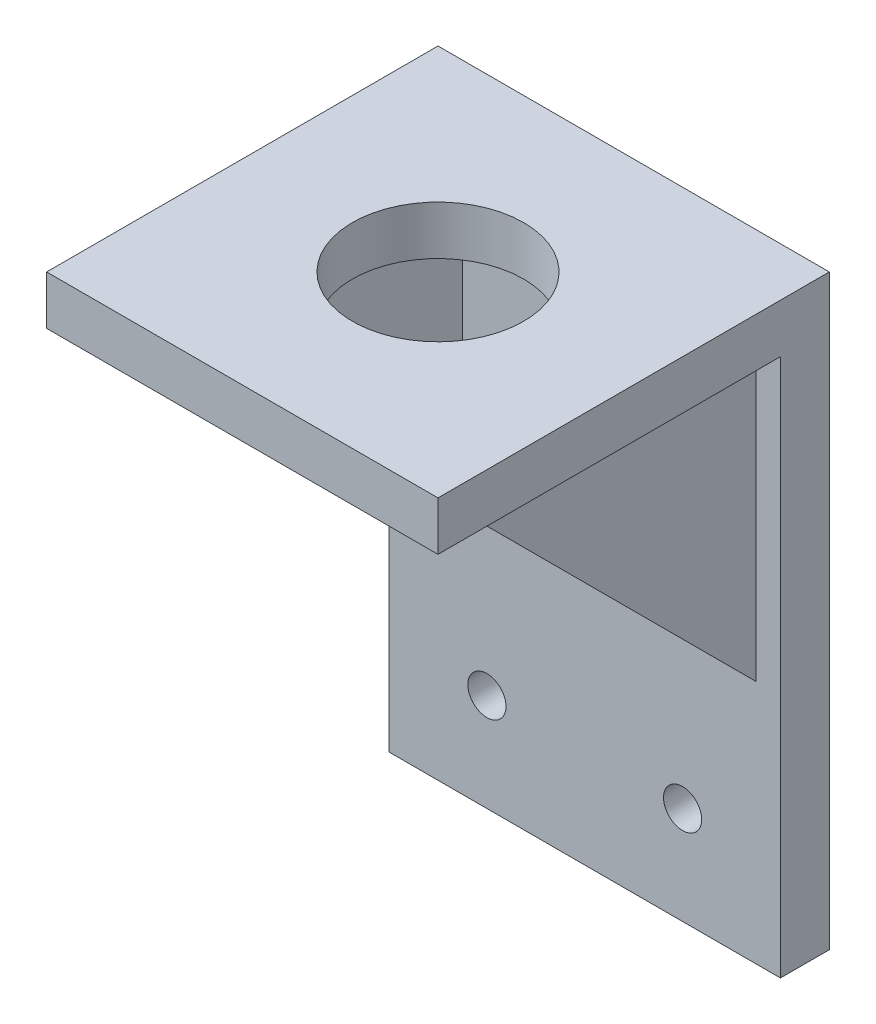
SolidWorks part; units mm, degrees
ref_plane "Front Plane" through (0, 0, 0) normal (0, 0, 1) x (1, 0, 0)
ref_plane "Top Plane" through (0, 0, 0) normal (0, 1, 0) x (1, 0, 0)
ref_plane "Right Plane" through (0, 0, 0) normal (1, 0, 0) x (0, 0, -1)
sketch "Sketch1" plane through (0, 0, 0) normal (0, 0, 1) x (1, 0, 0)
  line L1 (-25.4, -38.1) -> (25.4, -38.1)
  line L2 (-25.4, -38.1) -> (-25.4, 38.1)
  line L3 (-25.4, 38.1) -> (25.4, 38.1)
  line L4 (25.4, -38.1) -> (25.4, 38.1)
  line L5 (-25.4, -38.1) -> (25.4, 38.1) construction
  line L6 (-25.4, 38.1) -> (25.4, -38.1) construction
  circle A0 centre (-12.7, -25.4) radius 2.4765
  circle A1 centre (12.7, -25.4) radius 2.4765
  circle A2 centre (0, 25.4) radius 2.4765
  point P0 (0, 0)
  point P12 (0, 0)
  point P13 (0, 0)
  point P14 (0, 0)
  dimension "D3" = 4.953
  dimension "D1" = 50.8
  dimension "D2" = 76.2
  dimension "D4" = 12.7
  dimension "D5" = 12.7
  dimension "D6" = 12.7
  dimension "D7" = 12.7
extrude "Boss-Extrude1" add sketch "Sketch1" along normal blind 6.35
sketch "Sketch2" plane through (0, 0, 0) normal (0, 0, -1) x (-1, 0, 0)
  line L0 (-25.4, -38.1) -> (-25.4, 38.1) construction
  line L1 (25.4, 38.1) -> (25.4, -38.1) construction
  line L2 (-25.4, 38.1) -> (25.4, 38.1) construction
  arc A0 (-4.7625, 13.4704) -> (-9.2844, 10.8596) centre (0, 0) ccw
  arc A1 (-14.2576, 10.0826) -> (-15.8606, 7.3061) centre (0, 0) ccw
  arc A2 (4.7625, 13.4704) -> (3.3331, 15.4918) centre (5.4772, 15.4918) cw
  arc A3 (3.3331, 15.4918) -> (1.603, 17.3888) centre (1.4281, 15.4918) ccw
  arc A4 (-4.7625, 13.4704) -> (-3.3331, 15.4918) centre (-5.4772, 15.4918) ccw
  arc A5 (-1.603, 17.3888) -> (-3.3331, 15.4918) centre (-1.4281, 15.4918) ccw
  arc A6 (14.2576, 10.0826) -> (11.7497, 10.6325) centre (12.7022, 8.9827) ccw
  arc A7 (9.2844, 10.8596) -> (11.7497, 10.6325) centre (10.6777, 12.4893) ccw
  arc A8 (15.0829, 4.8593) -> (15.8606, 7.3061) centre (14.1304, 6.5091) ccw
  arc A9 (14.0469, 2.6107) -> (15.0829, 4.8593) centre (16.1549, 3.0025) cw
  arc A10 (15.8606, -7.3061) -> (15.0829, -4.8593) centre (14.1304, -6.5091) ccw
  arc A11 (14.0469, -2.6107) -> (15.0829, -4.8593) centre (16.1549, -3.0025) ccw
  arc A12 (11.7497, -10.6325) -> (14.2576, -10.0826) centre (12.7022, -8.9827) ccw
  arc A13 (9.2844, -10.8596) -> (11.7497, -10.6325) centre (10.6777, -12.4893) cw
  arc A14 (1.603, -17.3888) -> (3.3331, -15.4918) centre (1.4281, -15.4918) ccw
  arc A15 (4.7625, -13.4704) -> (3.3331, -15.4918) centre (5.4772, -15.4918) ccw
  arc A16 (-3.3331, -15.4918) -> (-1.603, -17.3888) centre (-1.4281, -15.4918) ccw
  arc A17 (-4.7625, -13.4704) -> (-3.3331, -15.4918) centre (-5.4772, -15.4918) cw
  arc A18 (-14.2576, -10.0826) -> (-11.7497, -10.6325) centre (-12.7022, -8.9827) ccw
  arc A19 (-9.2844, -10.8596) -> (-11.7497, -10.6325) centre (-10.6777, -12.4893) ccw
  arc A20 (-15.0829, -4.8593) -> (-15.8606, -7.3061) centre (-14.1304, -6.5091) ccw
  arc A21 (-14.0469, -2.6107) -> (-15.0829, -4.8593) centre (-16.1549, -3.0025) cw
  arc A22 (-15.8606, 7.3061) -> (-15.0829, 4.8593) centre (-14.1304, 6.5091) ccw
  arc A23 (-14.0469, 2.6107) -> (-15.0829, 4.8593) centre (-16.1549, 3.0025) ccw
  arc A24 (-11.7497, 10.6325) -> (-14.2576, 10.0826) centre (-12.7022, 8.9827) ccw
  arc A25 (-9.2844, 10.8596) -> (-11.7497, 10.6325) centre (-10.6777, 12.4893) cw
  arc A26 (1.603, 17.3888) -> (-1.603, 17.3888) centre (0, 0) ccw
  arc A27 (15.8606, 7.3061) -> (14.2576, 10.0826) centre (0, 0) ccw
  arc A28 (14.2576, -10.0826) -> (15.8606, -7.3061) centre (0, 0) ccw
  arc A29 (-1.603, -17.3888) -> (1.603, -17.3888) centre (0, 0) ccw
  arc A30 (-15.8606, -7.3061) -> (-14.2576, -10.0826) centre (0, 0) ccw
  arc A31 (-14.0469, 2.6107) -> (-14.0469, -2.6107) centre (0, 0) ccw
  arc A32 (-9.2844, -10.8596) -> (-4.7625, -13.4704) centre (0, 0) ccw
  arc A33 (4.7625, -13.4704) -> (9.2844, -10.8596) centre (0, 0) ccw
  arc A34 (14.0469, -2.6107) -> (14.0469, 2.6107) centre (0, 0) ccw
  arc A35 (9.2844, 10.8596) -> (4.7625, 13.4704) centre (0, 0) ccw
  circle A36 centre (-12.7, 25.4) radius 2.2225
  circle A37 centre (12.7, 25.4) radius 2.2225
  point P67 (0, 0)
  point P73 (0, 0)
  dimension "D1" = 28.575
  dimension "D2" = 34.925
  dimension "D4" = 1.905
  dimension "D9" = 4.445
  dimension "D3" = 9.525
  dimension "D6" = 12.7
  dimension "D7" = 12.7
  dimension "D8" = 12.7
  dimension "D5" = 6
extrude "Boss-Extrude2" add sketch "Sketch2" along normal blind 3.175
sketch "Sketch3" plane through (0, 0, -3.175) normal (0, 0, -1) x (-1, 0, 0)
  line L1 (-3.175, -1.5875) -> (3.175, -1.5875)
  line L2 (-3.175, -1.5875) -> (-3.175, 1.5875)
  line L3 (-3.175, 1.5875) -> (3.175, 1.5875)
  line L4 (3.175, -1.5875) -> (3.175, 1.5875)
  line L5 (-3.175, -1.5875) -> (3.175, 1.5875) construction
  line L6 (-3.175, 1.5875) -> (3.175, -1.5875) construction
  point P0 (0, 0)
  dimension "D1" = 6.35
  dimension "D2" = 3.175
extrude "Cut-Extrude1" cut sketch "Sketch3" against normal through all
sketch "Sketch4" plane through (0, 38.1, 0) normal (0, 1, 0) x (1, 0, 0)
  line L0 (25.4, 0) -> (-25.4, 0) construction
  line L1 (-25.4, -6.35) -> (25.4, -6.35)
  line L2 (-25.4, -6.35) -> (-25.4, -50.8)
  line L3 (-25.4, -50.8) -> (25.4, -50.8)
  line L4 (25.4, -6.35) -> (25.4, -50.8)
  dimension "D1" = 50.8
extrude "Boss-Extrude3" add sketch "Sketch4" against normal blind 6.35
sketch "Sketch5" plane through (0, 0, 0) normal (1, 0, 0) x (0, 0, -1)
  line L0 (-44.45, 31.75) -> (-6.35, -6.35)
  line L1 (-50.8, 31.75) -> (-6.35, 31.75) construction
  line L2 (-6.35, -38.1) -> (-6.35, 31.75) construction
  line L3 (-6.35, -6.35) -> (-6.35, 31.75)
  line L4 (-44.45, 31.75) -> (-6.35, 31.75)
  point P2 (-6.35, -9.8048)
  point P3 (-47.8696, 31.75)
  dimension "D1" = 38.1
extrude "Boss-Extrude4" add sketch "Sketch5" along normal mid plane 44.45
sketch "Sketch6" plane through (0, 0, 6.35) normal (0, 0, 1) x (1, 0, 0)
  line L0 (22.225, -6.35) -> (-22.225, -6.35) construction
  line L1 (-15.875, -6.35) -> (15.875, -6.35)
  line L2 (-15.875, -6.35) -> (-15.875, 31.75)
  line L3 (-15.875, 31.75) -> (15.875, 31.75)
  line L4 (15.875, -6.35) -> (15.875, 31.75)
  line L5 (22.225, 31.75) -> (-22.225, 31.75) construction
  line L7 (-22.225, 31.75) -> (-22.225, -6.35) construction
  point P8 (0, -6.35)
  dimension "D1" = 6.35
extrude "Cut-Extrude2" cut sketch "Sketch6" along normal through all
sketch "Sketch7" plane through (0, 31.75, 0) normal (0, -1, 0) x (1, 0, 0)
  line L0 (-25.4, 50.8) -> (25.4, 50.8) construction
  circle A0 centre (0, 25.4) radius 11.1125
  point P2 (0, 0)
  dimension "D2" = 22.225
  dimension "D1" = 25.4
extrude "Cut-Extrude3" cut sketch "Sketch7" against normal through all
